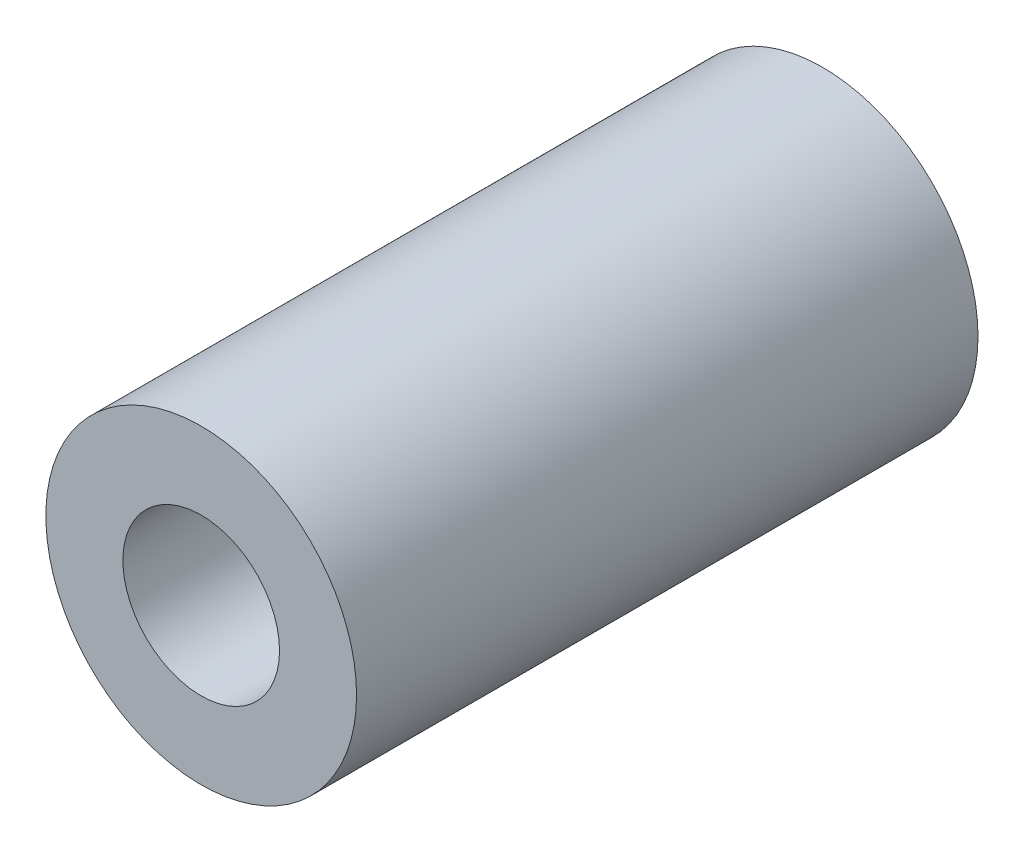
SolidWorks part; units mm, degrees
ref_plane "Front Plane" through (0, 0, 0) normal (0, 0, 1) x (1, 0, 0)
ref_plane "Top Plane" through (0, 0, 0) normal (0, 1, 0) x (1, 0, 0)
ref_plane "Right Plane" through (0, 0, 0) normal (1, 0, 0) x (0, 0, -1)
sketch "Sketch1" plane through (0, 0, 0) normal (0, 0, 1) x (1, 0, 0)
  line L0 (0, 3.2004) -> (0, 6.35) construction
  line L1 (0, -3.2004) -> (0, -6.35) construction
  circle A0 centre (0, 0) radius 6.35
  circle A1 centre (0, 0) radius 3.2004
  dimension "OD" = 12.7
  dimension "ID" = 6.4008
sketch "Sketch2" plane through (0, 0, 0) normal (1, 0, 0) x (0, 0, -1)
  line L0 (-12.7, 3.2004) -> (12.7, 3.2004) construction
  line L1 (-12.7, -3.2004) -> (12.7, -3.2004) construction
  line L2 (-12.7, -6.35) -> (12.7, -6.35) construction
  line L3 (-12.7, 6.35) -> (12.7, 6.35) construction
  dimension "Length" = 25.4
extrude "Extrude1" add sketch "Sketch1" along normal up to vertex (12.7 mm away) and the other way up to vertex (12.7 mm away) up to point (0, 3.2004, 12.7) other way up to point (0, 3.2004, -12.7)
sketch "Sketch3" plane through (0, 0, 12.7) normal (0, 0, 1) x (1, 0, 0)
  circle A0 centre (0, 0) radius 3.2004 construction
  circle A3 centre (0, 0) radius 3.2004
  point P3 (-3.2004, 0)
